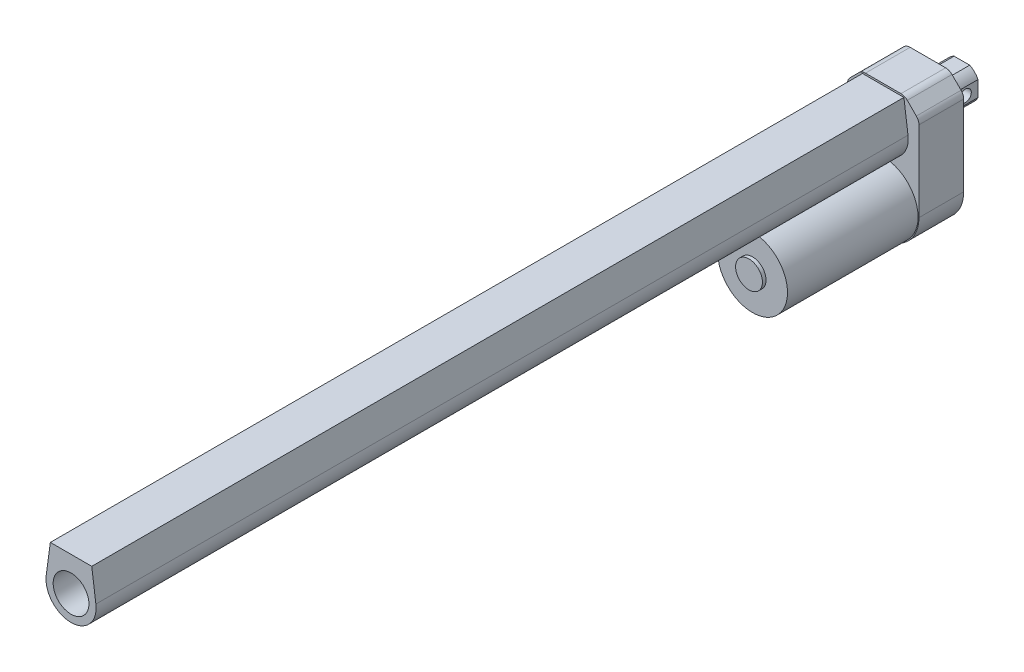
SolidWorks part; units mm, degrees
ref_plane "前视基准面" through (0, 0, 0) normal (0, 0, 1) x (1, 0, 0)
ref_plane "上视基准面" through (0, 0, 0) normal (0, 1, 0) x (1, 0, 0)
ref_plane "右视基准面" through (0, 0, 0) normal (1, 0, 0) x (0, 0, -1)
sketch "草图1" plane through (0, 0, 0) normal (0, 0, 1) x (1, 0, 0)
  line L0 (-20, 0) -> (-20, 44.9289)
  line L1 (-9.9289, 55) -> (9.9289, 55)
  line L2 (20, 44.9289) -> (20, 0)
  line L3 (-18.5355, 48.4645) -> (-13.4645, 53.5355)
  line L4 (13.4645, 53.5355) -> (18.5355, 48.4645)
  arc A0 (-20, 0) -> (20, 0) centre (0, 0) ccw
  arc A1 (-20, 44.9289) -> (-18.5355, 48.4645) centre (-15, 44.9289) cw
  arc A2 (20, 44.9289) -> (18.5355, 48.4645) centre (15, 44.9289) ccw
  arc A3 (13.4645, 53.5355) -> (9.9289, 55) centre (9.9289, 50) ccw
  arc A4 (-13.4645, 53.5355) -> (-9.9289, 55) centre (-9.9289, 50) cw
  point P4 (-20, 55)
  point P6 (20, 55)
  point P13 (-20, 47)
  point P16 (20, 47)
  point P19 (12, 55)
  point P22 (-12, 55)
  dimension "D1" = 40
  dimension "D2" = 55
  dimension "D3" = 5
  dimension "D4" = 5
extrude "凸台-拉伸1" add sketch "草图1" along normal blind 25
sketch "草图2" plane through (0, 0, 25) normal (0, 0, 1) x (1, 0, 0)
  circle A0 centre (0, 0) radius 19.5
  dimension "D1" = 39
extrude "凸台-拉伸2" add sketch "草图2" along normal blind 73
sketch "草图3" plane through (0, 0, 98) normal (0, 0, 1) x (1, 0, 0)
  circle A0 centre (0, 0) radius 7.5
  dimension "D1" = 15
extrude "凸台-拉伸3" add sketch "草图3" along normal blind 2
sketch "草图4" plane through (0, 0, 25) normal (0, 0, 1) x (1, 0, 0)
  line L0 (9.9289, 55) -> (-9.9289, 55) construction
  line L1 (-11.5765, 54) -> (-13.8757, 36.8615)
  line L3 (11.5765, 54) -> (13.8757, 36.8615)
  line L6 (0, 20.7202) -> (0, 56.7049) construction
  line L7 (-20, 44.9289) -> (-20, 0) construction
  line L8 (20, 0) -> (20, 44.9289) construction
  line L9 (-11.5765, 54) -> (11.5765, 54)
  arc A0 (-13.8757, 36.8615) -> (13.8757, 36.8615) centre (0, 35) ccw
  dimension "D1" = 28
  dimension "D2" = 20
  dimension "D3" = 1
extrude "凸台-拉伸4" add sketch "草图4" along normal blind 454
sketch "草图5" plane through (0, 0, 479) normal (0, 0, 1) x (1, 0, 0)
  circle A0 centre (0, 35) radius 10
  dimension "D1" = 20
extrude "切除-拉伸1" cut sketch "草图5" against normal blind 410
sketch "草图6" plane through (0, 0, 0) normal (0, 0, -1) x (-1, 0, 0)
  line L0 (-30.2846, 35) -> (34.2706, 35) construction
  line L1 (0, 69.8123) -> (0, -26.886) construction
  line L2 (-9.9289, 55) -> (9.9289, 55) construction
  line L4 (-4.3589, 44) -> (4.3589, 44)
  line L5 (-9, 39.3589) -> (-9, 30.6411)
  line L6 (-4.3589, 26) -> (4.3589, 26)
  line L7 (9, 39.3589) -> (9, 30.6411)
  arc A0 (-4.3589, 44) -> (-9, 39.3589) centre (0, 35) ccw
  arc A1 (9, 39.3589) -> (4.3589, 44) centre (0, 35) ccw
  arc A2 (-9, 30.6411) -> (-4.3589, 26) centre (0, 35) ccw
  arc A3 (4.3589, 26) -> (9, 30.6411) centre (0, 35) ccw
  dimension "D3" = 20
  dimension "D1" = 20
  dimension "D2" = 18
  dimension "D4" = 18
extrude "凸台-拉伸5" add sketch "草图6" along normal blind 19
sketch "草图7" plane through (9, 0, 0) normal (1, 0, 0) x (0, 0, -1)
  line L0 (26.7064, 35) -> (-8.4403, 35) construction
  line L2 (19, 44) -> (0, 44) construction
  line L3 (19, 26) -> (0, 26) construction
  line L4 (19, 39.3589) -> (19, 30.6411) construction
  circle A0 centre (12, 35) radius 3.25
  dimension "D1" = 6.5
  dimension "D2" = 7
extrude "切除-拉伸2" cut sketch "草图7" against normal blind 19
